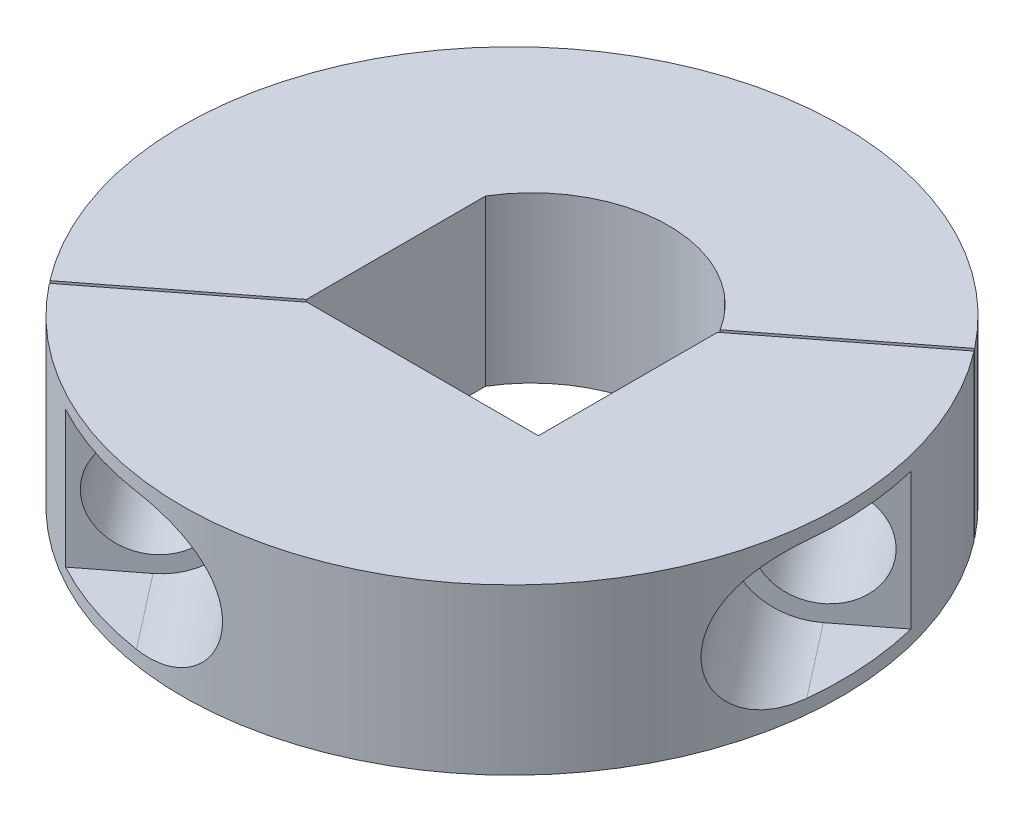
SolidWorks part; units mm, degrees
ref_plane "Front Plane" through (0, 0, 0) normal (0, 0, 1) x (1, 0, 0)
ref_plane "Top Plane" through (0, 0, 0) normal (0, 1, 0) x (1, 0, 0)
ref_plane "Right Plane" through (0, 0, 0) normal (1, 0, 0) x (0, 0, -1)
sketch "Sketch1" plane through (0, 0, 0) normal (0, 1, 0) x (1, 0, 0)
  circle A0 centre (0, 0) radius 25.4
  dimension "D1" = 50.8
extrude "Boss-Extrude1" add sketch "Sketch1" along normal blind 12.7
sketch "Sketch2" plane through (0, 12.7, 0) normal (0, 1, 0) x (1, 0, 0)
  line L1 (-9.017, -6.985) -> (9.017, -6.985)
  line L2 (-9.017, -6.985) -> (-9.017, 6.985)
  line L4 (9.017, -6.985) -> (9.017, 6.985)
  line L5 (-9.017, -6.985) -> (9.017, 6.985) construction
  line L6 (-9.017, 6.985) -> (9.017, -6.985) construction
  arc A0 (-9.017, 6.985) -> (9.017, 6.985) centre (0, 1.5224) cw
  point P0 (0, 0)
  point P7 (0, 12.065)
  dimension "D1" = 19.05
  dimension "D2" = 13.97
  dimension "D3" = 18.034
extrude "Cut-Extrude1" cut sketch "Sketch2" along direction (0, 1, 0) on the side against the normal through all
sketch "Sketch4" plane through (0, 12.7, 0) normal (0, 1, 0) x (1, 0, 0)
  line L0 (20.08, 15.5549) -> (-20.08, -15.5549) construction
  line L1 (20.0019, 15.6551) -> (-20.1575, -15.4543)
  line L2 (-20.0019, -15.6551) -> (20.1575, 15.4543)
  circle A0 centre (0, 0) radius 25.4 construction
  arc A1 (20.0019, 15.6551) -> (20.1575, 15.4543) centre (0, 0) cw
  arc A2 (-20.1575, -15.4543) -> (-20.0019, -15.6551) centre (0, 0) ccw
  dimension "D1" = 0.254
  dimension "D2" = 0.127
extrude "Cut-Extrude5" cut sketch "Sketch4" along direction (0, 1, 0) on the side against the normal through all
ref_plane "Plane1" through (6.2997, 0, 8.1324) normal (-0.6124, 0, -0.7905) x (-0.7905, 0, 0.6124)
sketch "Sketch5" plane through (6.2997, 0, 8.1324) normal (-0.6124, 0, -0.7905) x (-0.7905, 0, 0.6124)
  line L1 (-11.4198, 12.7) -> (-25.3997, 12.7) construction
  line L2 (-11.4198, 12.7) -> (-11.4198, 0) construction
  line L3 (-11.4198, 0) -> (-25.3997, 0) construction
  line L4 (-25.3997, 12.7) -> (-25.3997, 0) construction
  line L5 (-11.4198, 12.7) -> (-25.3997, 0) construction
  line L6 (-11.4198, 0) -> (-25.3997, 12.7) construction
  line L7 (0, -30.9944) -> (0, 40.6496) construction
  circle A0 centre (-18.4097, 6.35) radius 4
  circle A1 centre (18.4097, 6.35) radius 4
  point P0 (-18.4097, 6.35)
  dimension "D1" = 8
extrude "Cut-Extrude6" cut sketch "Sketch5" against normal through all both and the other way through all
sketch "Sketch6" plane through (6.2997, 0, 8.1324) normal (-0.6124, 0, -0.7905) x (-0.7905, 0, 0.6124)
  line L0 (-18.4097, 1.08) -> (-23.2236, 1.08)
  line L1 (-23.2236, 0) -> (-23.2236, 12.7) construction
  line L4 (-18.4097, 11.62) -> (-23.2236, 11.62)
  line L5 (-23.2236, 1.08) -> (-23.2236, 11.62)
  line L6 (25.3997, 12.7) -> (-25.3997, 12.7) construction
  line L7 (-25.3997, 0) -> (25.3997, 0) construction
  line L8 (0, 26.0428) -> (0, -26.8891) construction
  line L9 (23.2236, 0) -> (23.2236, 12.7) construction
  line L10 (23.2236, 1.08) -> (23.2236, 11.62)
  line L11 (18.4097, 1.08) -> (23.2236, 1.08)
  line L12 (18.4097, 11.62) -> (23.2236, 11.62)
  arc A0 (-18.4097, 1.08) -> (-18.4097, 11.62) centre (-18.4097, 6.35) ccw
  circle A1 centre (-18.4097, 6.35) radius 4 construction
  arc A2 (18.4097, 1.08) -> (18.4097, 11.62) centre (18.4097, 6.35) cw
  dimension "D1" = 1.27
extrude "Cut-Extrude7" cut sketch "Sketch6" against normal through all
